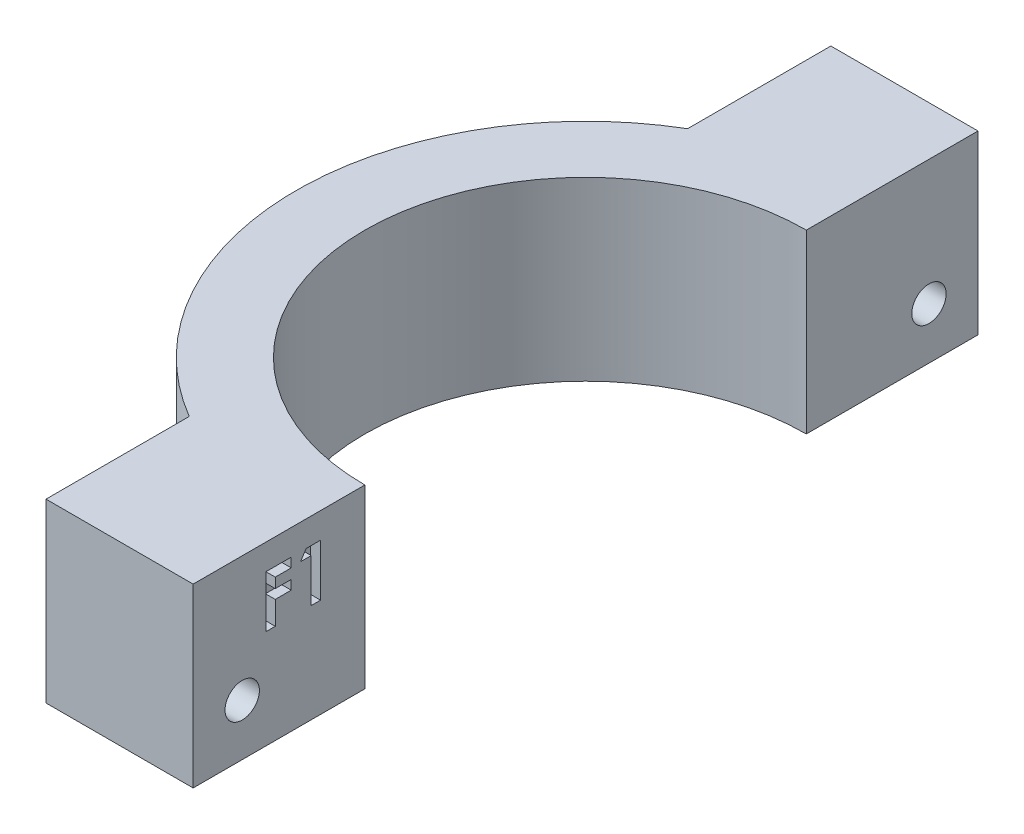
SolidWorks part; units mm, degrees
ref_plane "Front Plane" through (0, 0, 0) normal (0, 0, 1) x (1, 0, 0)
ref_plane "Top Plane" through (0, 0, 0) normal (0, 1, 0) x (1, 0, 0)
ref_plane "Right Plane" through (0, 0, 0) normal (1, 0, 0) x (0, 0, -1)
sketch "Sketch1" plane through (0, 0, 0) normal (0, 1, 0) x (1, 0, 0)
  line L0 (-46.9983, 32.5286) -> (-46.9983, -47.4714)
  line L1 (-46.9983, -47.4714) -> (-16.9983, -47.4714)
  line L2 (-16.9983, -47.4714) -> (-16.9983, -29.9714)
  line L3 (-46.9983, 32.5286) -> (-16.9983, 32.5286)
  line L4 (-16.9983, 32.5286) -> (-16.9983, 15.0286)
  line L5 (-31.9983, -47.4714) -> (-31.9983, -32.8732)
  line L6 (-31.9983, 32.5286) -> (-31.9983, 17.9303)
  arc A0 (-16.9983, 15.0286) -> (-16.9983, -29.9714) centre (-16.9983, -7.4714) ccw
  arc A1 (-16.9983, 22.0286) -> (-16.9983, -36.9714) centre (-16.9983, -7.4714) ccw
  dimension "D1" = 80
  dimension "D2" = 30
  dimension "D3" = 30
  dimension "D4" = 45
  dimension "D5" = 17.5
  dimension "D6" = 17.5
  dimension "D7" = 7
extrude "Boss-Extrude1" add sketch "Sketch1" along normal blind 18 contours L4 A1 L2 A0 | A1 L4 L3 L6 | A1 L5 L1 L2
sketch "Sketch2" plane through (-16.9983, 0, 0) normal (1, 0, 0) x (0, 0, -1)
  line L0 (-47.4714, 18) -> (-47.4714, 0) construction
  line L1 (32.5286, 18) -> (15.0286, 18) construction
  line L3 (32.5286, 18) -> (32.5286, 0) construction
  line L8 (-47.4714, 18) -> (-29.9714, 18) construction
  circle A0 centre (-42.4714, 5.25) radius 1.75
  circle A1 centre (27.5286, 5.25) radius 1.75
  dimension "D3" = 12.75
  dimension "D5" = 3.5
  dimension "D6" = 3.5
  dimension "D1" = 5
  dimension "D2" = 5
  dimension "D4" = 12.75
extrude "Cut-Extrude1" cut sketch "Sketch2" against normal through all
sketch "Sketch3" plane through (-16.9983, 0, 0) normal (1, 0, 0) x (0, 0, -1)
  text T0 "<b>F1</b>" font "Century Gothic" height in points 20
extrude "Cut-Extrude2" cut sketch "Sketch3" against normal blind 1
sketch "Sketch4" plane through (-31.9983, 0, 0) normal (-1, 0, 0) x (0, 0, 1)
  line L1 (-26.3087, 2.3182) -> (-24.3797, 4.8405)
  line L2 (-24.3797, 4.8405) -> (-25.5995, 7.7723)
  line L3 (-25.5995, 7.7723) -> (-28.7484, 8.1818)
  line L4 (-28.7484, 8.1818) -> (-30.6775, 5.6595)
  line L5 (-30.6775, 5.6595) -> (-29.4577, 2.7277)
  line L6 (-29.4577, 2.7277) -> (-26.3087, 2.3182)
  line L7 (43.8236, 2.3768) -> (45.6357, 4.9844)
  line L8 (45.6357, 4.9844) -> (44.2836, 7.8576)
  line L9 (44.2836, 7.8576) -> (41.1193, 8.1232)
  line L10 (41.1193, 8.1232) -> (39.3071, 5.5156)
  line L11 (39.3071, 5.5156) -> (40.6593, 2.6424)
  line L12 (40.6593, 2.6424) -> (43.8236, 2.3768)
  circle A0 centre (-27.5286, 5.25) radius 2.75 construction
  circle A1 centre (42.4714, 5.25) radius 2.75 construction
extrude "Cut-Extrude3" cut sketch "Sketch4" against normal blind 5
